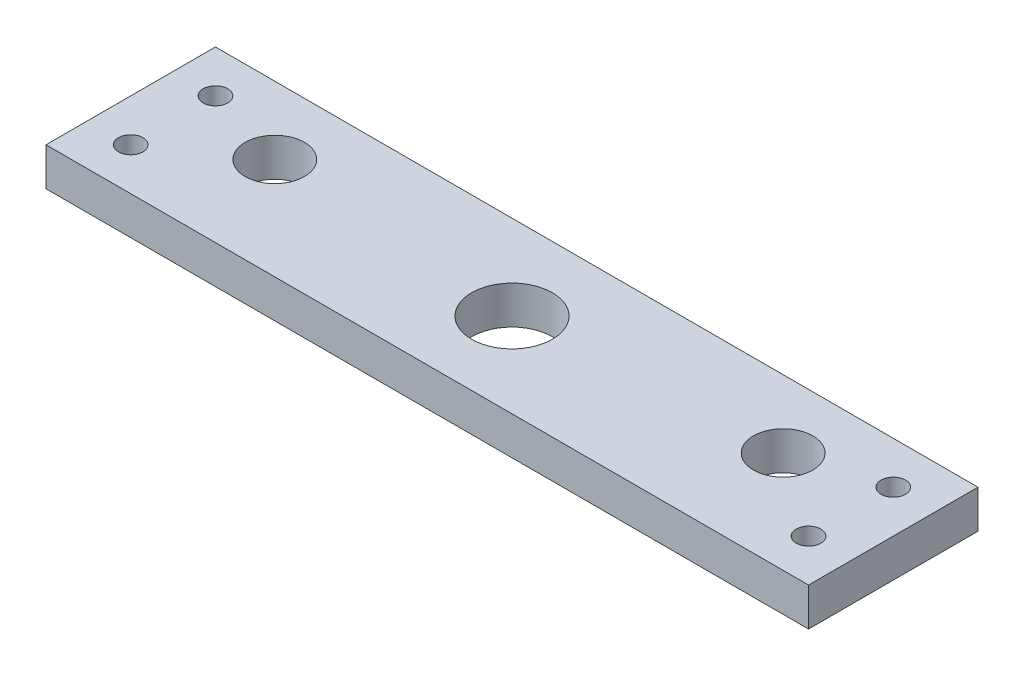
SolidWorks part; units mm, degrees
ref_plane "Front Plane" through (0, 0, 0) normal (0, 0, 1) x (1, 0, 0)
ref_plane "Top Plane" through (0, 0, 0) normal (0, 1, 0) x (1, 0, 0)
ref_plane "Right Plane" through (0, 0, 0) normal (1, 0, 0) x (0, 0, -1)
sketch "Sketch1" plane through (0, 0, 0) normal (0, 1, 0) x (1, 0, 0)
  line L0 (0, 4.7625) -> (0, 10)
  line L1 (-45, -10) -> (0, -10)
  line L2 (-45, -10) -> (-45, 10)
  line L3 (-45, 10) -> (0, 10)
  line L4 (0, -10) -> (0, -4.7625)
  line L5 (0, -4.7625) -> (0, 4.7625) construction
  circle A0 centre (-40, 5) radius 1.45
  circle A1 centre (-40, -5) radius 1.45
  arc A2 (0, 4.7625) -> (0, -4.7625) centre (0, 0) ccw
  dimension "D3" = 2.9
  dimension "D7" = 4.7625
  dimension "D1" = 20
  dimension "D2" = 45
  dimension "D4" = 10
  dimension "D5" = 5
  dimension "D6" = 5
extrude "Boss-Extrude1" add sketch "Sketch1" along normal blind 4.5
mirror "Mirror1" about plane through (0, 4.5, 10) normal (-1, 0, 0) of "Boss-Extrude1"
sketch "Sketch2" plane through (0, 4.5, 0) normal (0, 1, 0) x (1, 0, 0)
  line L0 (-30, 2) -> (30, 2) construction
  line L1 (0, 2) -> (0, 0) construction
  circle A0 centre (-30, 2) radius 3.5
  circle A2 centre (30, 2) radius 3.5
  dimension "D2" = 7
  dimension "D1" = 2
  dimension "D3" = 30
extrude "Cut-Extrude1" cut sketch "Sketch2" against normal through all
